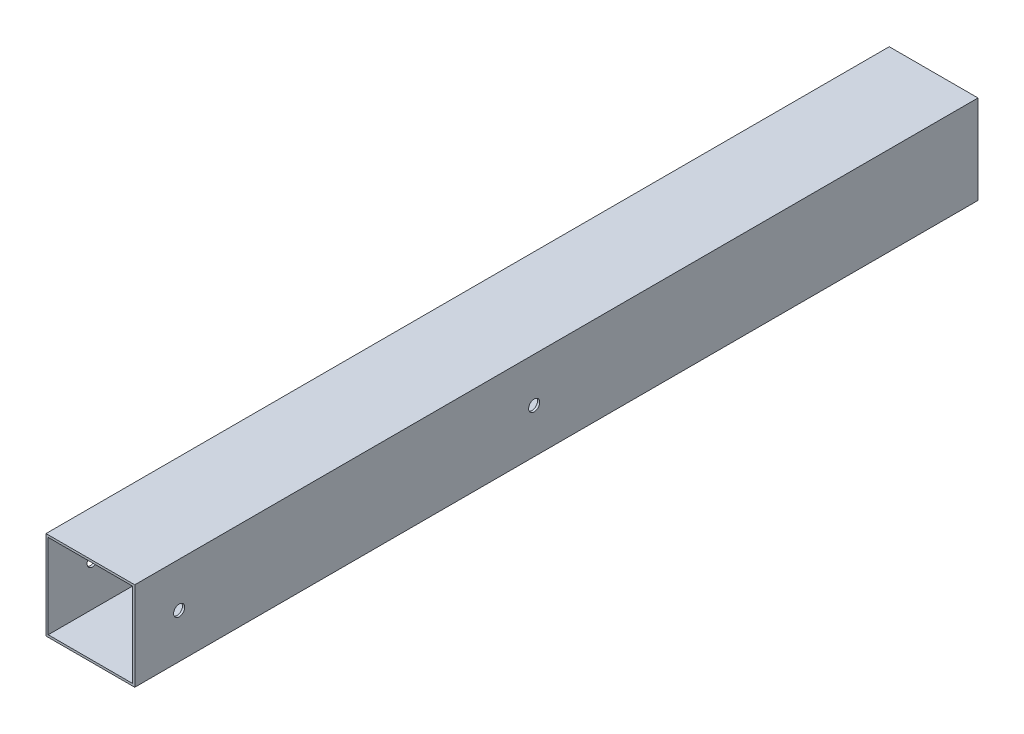
SolidWorks part; units mm, degrees
material "3.0205 (EN-AW 1200)"
ref_plane "Piano frontale" through (0, 0, 0) normal (0, 0, 1) x (1, 0, 0)
ref_plane "Piano superiore" through (0, 0, 0) normal (0, 1, 0) x (1, 0, 0)
ref_plane "Piano destro" through (0, 0, 0) normal (1, 0, 0) x (0, 0, -1)
sketch "Schizzo1" plane through (0, 0, 0) normal (0, 0, 1) x (1, 0, 0)
  line L1 (-20, 20) -> (20, 20)
  line L2 (-20, 20) -> (-20, -20)
  line L3 (-20, -20) -> (20, -20)
  line L4 (20, 20) -> (20, -20)
  line L5 (-20, 20) -> (20, -20) construction
  line L6 (-20, -20) -> (20, 20) construction
  line L7 (19, -19) -> (-19, -19)
  line L8 (19, -19) -> (19, 19)
  line L9 (19, 19) -> (-19, 19)
  line L10 (-19, -19) -> (-19, 19)
  line L11 (19, -19) -> (-19, 19) construction
  line L12 (19, 19) -> (-19, -19) construction
  point P0 (0, 0)
  point P6 (0, 0)
  dimension "D1" = 40
  dimension "D2" = 40
  dimension "D3" = 38
extrude "Estrusione-Estrusione2" add sketch "Schizzo1" along normal blind 380
sketch "Schizzo2" plane through (20, 0, 0) normal (1, 0, 0) x (0, 0, -1)
  line L0 (-380, -20) -> (-380, 20) construction
  line L1 (0, -20) -> (0, 20) construction
  line L2 (-380, 20) -> (0, 20) construction
  circle A0 centre (-360, 0) radius 2.5
  circle A1 centre (-200, 0) radius 2.5
  dimension "D1" = 5
  dimension "D2" = 5
  dimension "D3" = 20
  dimension "D4" = 200
  dimension "D5" = 20
  dimension "D6" = 20
extrude "Taglio-Estrusione1" cut sketch "Schizzo2" against normal through all
